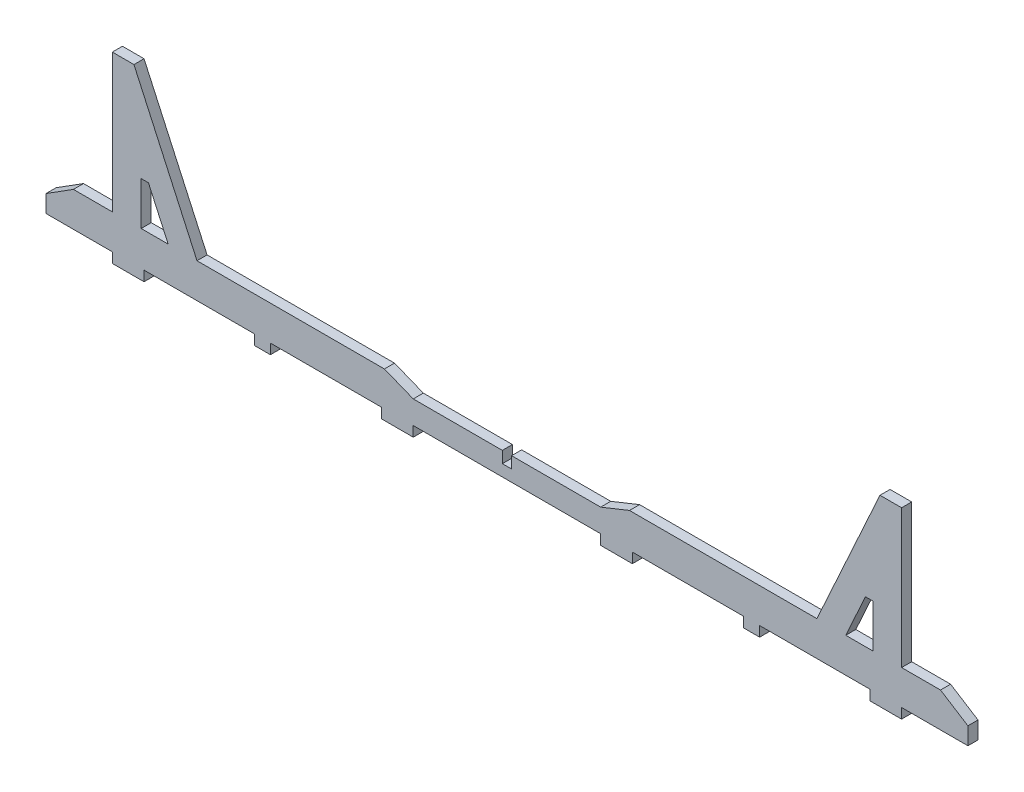
SolidWorks part; units mm, degrees
ref_plane "Front Plane" through (0, 0, 0) normal (0, 0, 1) x (1, 0, 0)
ref_plane "Top Plane" through (0, 0, 0) normal (0, 1, 0) x (1, 0, 0)
ref_plane "Right Plane" through (0, 0, 0) normal (1, 0, 0) x (0, 0, -1)
sketch "Sketch1" plane through (0, 0, 0) normal (0, 0, 1) x (1, 0, 0)
  line L0 (0, 0) -> (49.5354, 0) construction
  line L1 (104.371, 0) -> (104.371, 60) construction
  line L5 (0, 12) -> (75, 12) construction
  line L6 (75, 12) -> (96.871, 60)
  line L7 (96.871, 60) -> (104.371, 60)
  line L8 (0, 0) -> (0, -3.5)
  line L9 (0, -3.5) -> (11, -3.5)
  line L10 (11, -3.5) -> (11, 0)
  line L11 (11, 0) -> (49.5354, 0)
  line L12 (93.371, 0) -> (93.371, -3.5)
  line L13 (93.371, -3.5) -> (104.371, -3.5)
  line L14 (104.371, -3.5) -> (104.371, 0)
  line L15 (0, 8) -> (10, 12)
  line L16 (49.5354, 0) -> (49.5354, -3.5) construction
  line L17 (49.5354, -3.5) -> (55.1354, -3.5) construction
  line L18 (55.1354, -3.5) -> (55.1354, 0) construction
  line L19 (49.5354, 0) -> (49.5354, -3.5)
  line L20 (49.5354, -3.5) -> (55.1354, -3.5)
  line L21 (55.1354, -3.5) -> (55.1354, 0)
  line L22 (55.1354, 0) -> (104.371, 0) construction
  line L23 (55.1354, 0) -> (93.371, 0)
  line L24 (0, 0) -> (0, 8) construction
  line L25 (75, 12) -> (10, 12)
  line L26 (75, 12) -> (104.371, 12) construction
  line L28 (85, 12) -> (91.8347, 27)
  line L29 (75, 12) -> (85, 12) construction
  line L30 (82.1336, 12) -> (100.0982, 12) construction
  line L31 (104.371, 12) -> (94.371, 12) construction
  line L35 (94.371, 12) -> (94.371, 27) construction
  line L36 (91.8347, 27) -> (85, 12) construction
  line L37 (85, 12) -> (94.371, 12)
  line L38 (94.371, 27) -> (94.371, 12)
  line L39 (0, 0) -> (-65, 0)
  line L40 (0, 8) -> (-30.9, 8)
  line L41 (-65, 8) -> (-65, 0) construction
  line L42 (-65, 4) -> (0, 4) construction
  line L43 (-32.5, 8) -> (-32.5, 0) construction
  line L44 (-156.8347, 27) -> (-150, 12) construction
  line L45 (-159.371, 12) -> (-159.371, 27) construction
  line L46 (-169.371, 12) -> (-159.371, 12) construction
  line L47 (-147.1336, 12) -> (-165.0982, 12) construction
  line L48 (-140, 12) -> (-150, 12) construction
  line L49 (-140, 12) -> (-169.371, 12) construction
  line L50 (-65, 0) -> (-65, 8) construction
  line L51 (-120.1354, 0) -> (-169.371, 0) construction
  line L52 (-120.1354, -3.5) -> (-120.1354, 0) construction
  line L53 (-114.5354, -3.5) -> (-120.1354, -3.5) construction
  line L54 (-114.5354, 0) -> (-114.5354, -3.5) construction
  line L55 (-65, 12) -> (-140, 12) construction
  line L56 (-65, 0) -> (-65, 12) construction
  line L57 (-65, 60) -> (-65, 0) construction
  line L58 (-169.371, 60) -> (-65, 60) construction
  line L59 (-65, 0) -> (-114.5354, 0) construction
  line L61 (-150, 12) -> (-159.371, 12)
  line L62 (-150, 12) -> (-156.8347, 27)
  line L64 (-140, 12) -> (-75, 12)
  line L65 (-120.1354, 0) -> (-158.371, 0)
  line L66 (-120.1354, -3.5) -> (-120.1354, 0)
  line L67 (-114.5354, -3.5) -> (-120.1354, -3.5)
  line L68 (-114.5354, 0) -> (-114.5354, -3.5)
  line L69 (-65, 8) -> (-75, 12)
  line L70 (-169.371, -3.5) -> (-169.371, 0)
  line L71 (-158.371, -3.5) -> (-169.371, -3.5)
  line L72 (-158.371, 0) -> (-158.371, -3.5)
  line L73 (-76, 0) -> (-114.5354, 0)
  line L74 (-76, -3.5) -> (-76, 0)
  line L75 (-65, -3.5) -> (-76, -3.5)
  line L76 (-65, 0) -> (-65, -3.5)
  line L77 (-161.871, 60) -> (-169.371, 60)
  line L78 (-140, 12) -> (-161.871, 60)
  line L79 (-169.371, 12) -> (-169.371, 60)
  line L80 (104.371, 12) -> (108.371, 12)
  line L82 (112.371, 0) -> (104.371, 0)
  line L83 (104.371, 60) -> (104.371, 12)
  line L86 (-177.371, 0) -> (-169.371, 0)
  line L87 (-169.371, 12) -> (-173.371, 12)
  line L89 (94.371, 27) -> (91.8347, 27)
  line L90 (-159.371, 27) -> (-156.8347, 27)
  line L91 (-159.371, 27) -> (-159.371, 12)
  line L93 (-34.1, 8) -> (-34.1, 4)
  line L94 (-34.1, 4) -> (-30.9, 4)
  line L95 (-30.9, 4) -> (-30.9, 8)
  line L96 (-34.1, 8) -> (-65, 8)
  line L97 (-173.371, 12) -> (-182.871, 12)
  line L98 (-192.371, 6) -> (-192.371, 0)
  line L99 (-192.371, 0) -> (-177.371, 0)
  line L100 (-192.371, 6) -> (-182.871, 12)
  line L101 (127.371, 6) -> (117.871, 12)
  line L102 (127.371, 0) -> (112.371, 0)
  line L103 (127.371, 6) -> (127.371, 0)
  line L104 (108.371, 12) -> (117.871, 12)
  point P17 (52.1854, 0)
  point P36 (-32.5, 4)
  point P61 (-117.1854, 0)
  dimension "D1" = 104.371
  dimension "D2" = 60
  dimension "D3" = 75
  dimension "D4" = 12
  dimension "D5" = 3.5
  dimension "D6" = 3.5
  dimension "D7" = 11
  dimension "D8" = 11
  dimension "D9" = 5.6
  dimension "D10" = 3.5
  dimension "D11" = 7.5
  dimension "D12" = 10
  dimension "D13" = 10
  dimension "D14" = 65
  dimension "D15" = 8
  dimension "D16" = 8
  dimension "D17" = 15
  dimension "D18" = 3.2
  dimension "D19" = 15
extrude "Boss-Extrude1" add sketch "Sketch1" along normal blind 3.5
